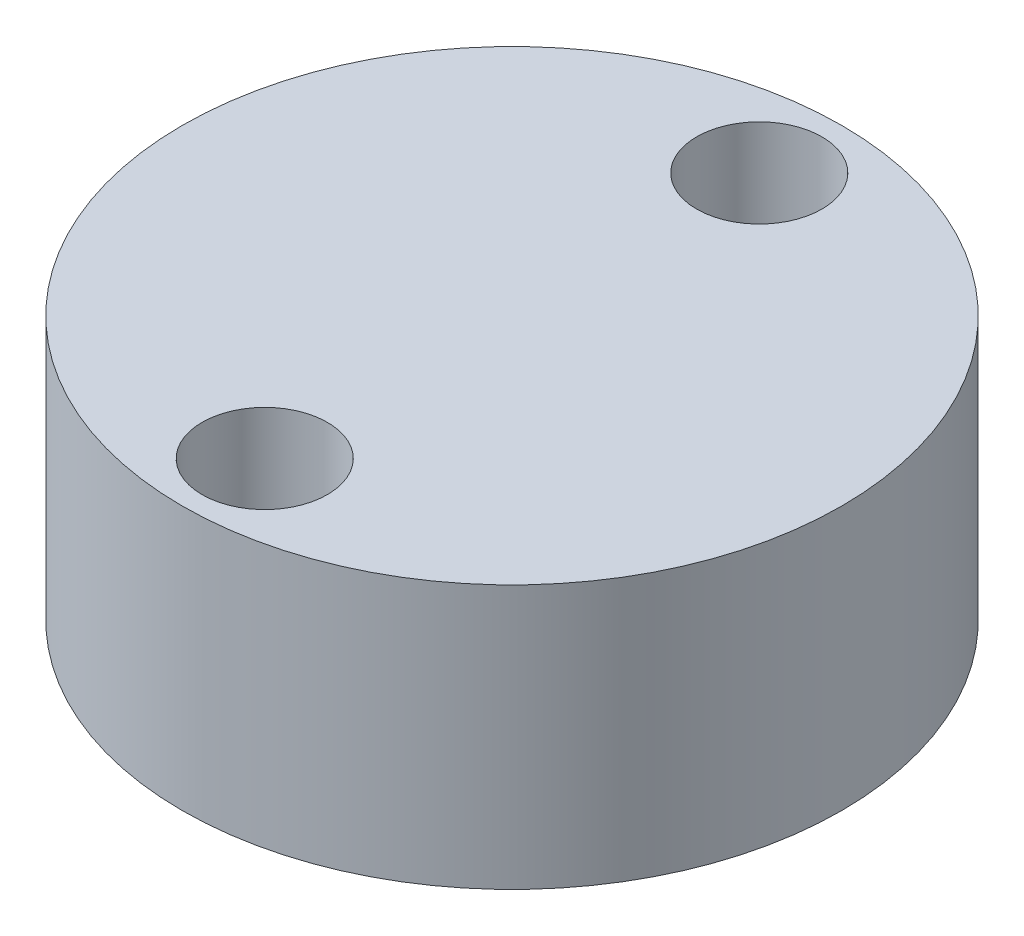
SolidWorks part; units mm, degrees
ref_plane "Front Plane" through (0, 0, 0) normal (0, 0, 1) x (1, 0, 0)
ref_plane "Top Plane" through (0, 0, 0) normal (0, 1, 0) x (1, 0, 0)
ref_plane "Right Plane" through (0, 0, 0) normal (1, 0, 0) x (0, 0, -1)
sketch "Sketch1" plane through (0, 0, 0) normal (0, 1, 0) x (1, 0, 0)
  line L0 (0, 3.75) -> (0, -3.75) construction
  circle A0 centre (0, 0) radius 5
  circle A1 centre (0, 3.75) radius 0.5
  circle A2 centre (0, -3.75) radius 0.5
  point P7 (0, 0)
  dimension "D1" = 10
  dimension "D3" = 1
  dimension "D2" = 7.5
extrude "Boss-Extrude1" add sketch "Sketch1" along normal blind 4
sketch "Sketch2" plane through (0, 4, 0) normal (0, 1, 0) x (1, 0, 0)
  circle A0 centre (0, 3.75) radius 0.95
  circle A1 centre (0, -3.75) radius 0.95
  dimension "D1" = 1.9
extrude "Cut-Extrude1" cut sketch "Sketch2" against normal blind 2
